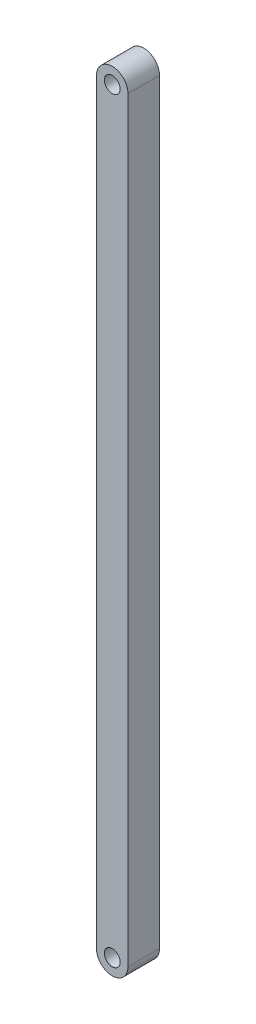
SolidWorks part; units mm, degrees
material "Alloy Steel"
ref_plane "Front Plane" through (0, 0, 0) normal (0, 0, 1) x (1, 0, 0)
ref_plane "Top Plane" through (0, 0, 0) normal (0, 1, 0) x (1, 0, 0)
ref_plane "Right Plane" through (0, 0, 0) normal (1, 0, 0) x (0, 0, -1)
sketch "Sketch1" plane through (0, 0, 0) normal (0, 0, 1) x (1, 0, 0)
  line L0 (0, 0) -> (0, 480)
  line L1 (20, 480) -> (20, 0)
  arc A0 (0, 480) -> (20, 480) centre (10, 480) cw
  arc A1 (20, 0) -> (0, 0) centre (10, 0) cw
  point P7 (0, 240)
  dimension "D1" = 480
  dimension "D2" = 20
extrude "Boss-Extrude1" add sketch "Sketch1" along normal blind 20
hole_wizard "Ø10.0mm Dowel Hole1" positions "Sketch2" profile "Sketch3" hole size "Ø10.0" standard "ANSI Metric" end condition up to next
sketch "Sketch2" plane through (0, 0, 20) normal (0, 0, 1) x (1, 0, 0)
  point P0 (10, 480)
  point P3 (10, 0)
sketch "Sketch3" plane through (10, 480, 20) normal (1, 0, 0) x (0, -1, 0)
  line L0 (0, 0) -> (0, 20)
  line L1 (0, 20) -> (5, 20)
  line L2 (5, 20) -> (5, 0.025)
  line L3 (5, 0.025) -> (5.025, 0)
  line L5 (5.025, 0) -> (0, 0)
  line L6 (-5, 0.025) -> (-5.025, 0) construction
  line L11 (0, -6.35) -> (0, 107.95) construction
  dimension "Thru Hole Dia." = 10
  dimension "Thru Hole Depth" = 20
  dimension "Near C'Sink Dia." = 10.05
  dimension "Near C'Sink Angle" = 90
